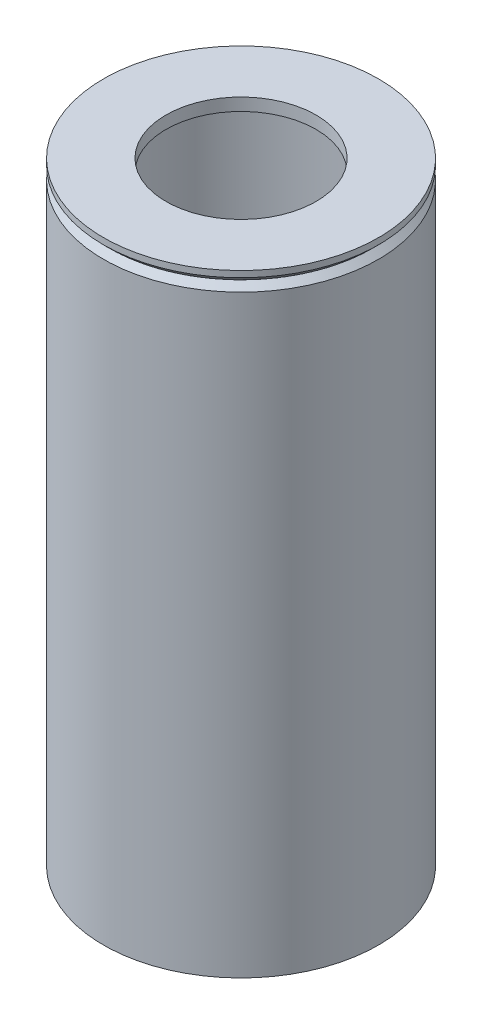
SolidWorks part; units mm, degrees
ref_plane "Front Plane" through (0, 0, 0) normal (0, 0, 1) x (1, 0, 0)
ref_plane "Top Plane" through (0, 0, 0) normal (0, 1, 0) x (1, 0, 0)
ref_plane "Right Plane" through (0, 0, 0) normal (1, 0, 0) x (0, 0, -1)
sketch "Sketch1" plane through (0, 0, 0) normal (0, 0, 1) x (1, 0, 0)
  line L0 (0, 0) -> (0, 109.341) construction
  line L1 (-69.85, 0) -> (-69.85, -304.8)
  line L2 (-69.85, -304.8) -> (-63.5, -304.8)
  line L3 (-63.5, -304.8) -> (-63.5, 0)
  line L4 (-63.5, 0) -> (-69.85, 0)
  point P4 (0, 0)
  dimension "D1" = 304.8
  dimension "D2" = 6.35
  dimension "D3" = 63.5
revolve "Revolve1" add sketch "Sketch1" angle 360 about L0
sketch "Sketch2" plane through (0, 0, 0) normal (0, 0, 1) x (1, 0, 0)
  line L0 (-69.85, 6.35) -> (-38.1, 6.35)
  line L1 (-38.1, 6.35) -> (-38.1, 0)
  line L2 (-38.1, 0) -> (-69.85, 0)
  line L3 (-69.85, 0) -> (-69.85, 6.35)
  point P2 (0, 0)
  dimension "D1" = 6.35
  dimension "D2" = 38.1
revolve "Revolve2" add sketch "Sketch2" angle 360 about L0
chamfer "Chamfer1" distance 3.175 angle 45 1 edges at (0, 0, -69.85)
chamfer "Chamfer2" distance 3.175 angle 45 1 edges at (0, 0, -69.85)
